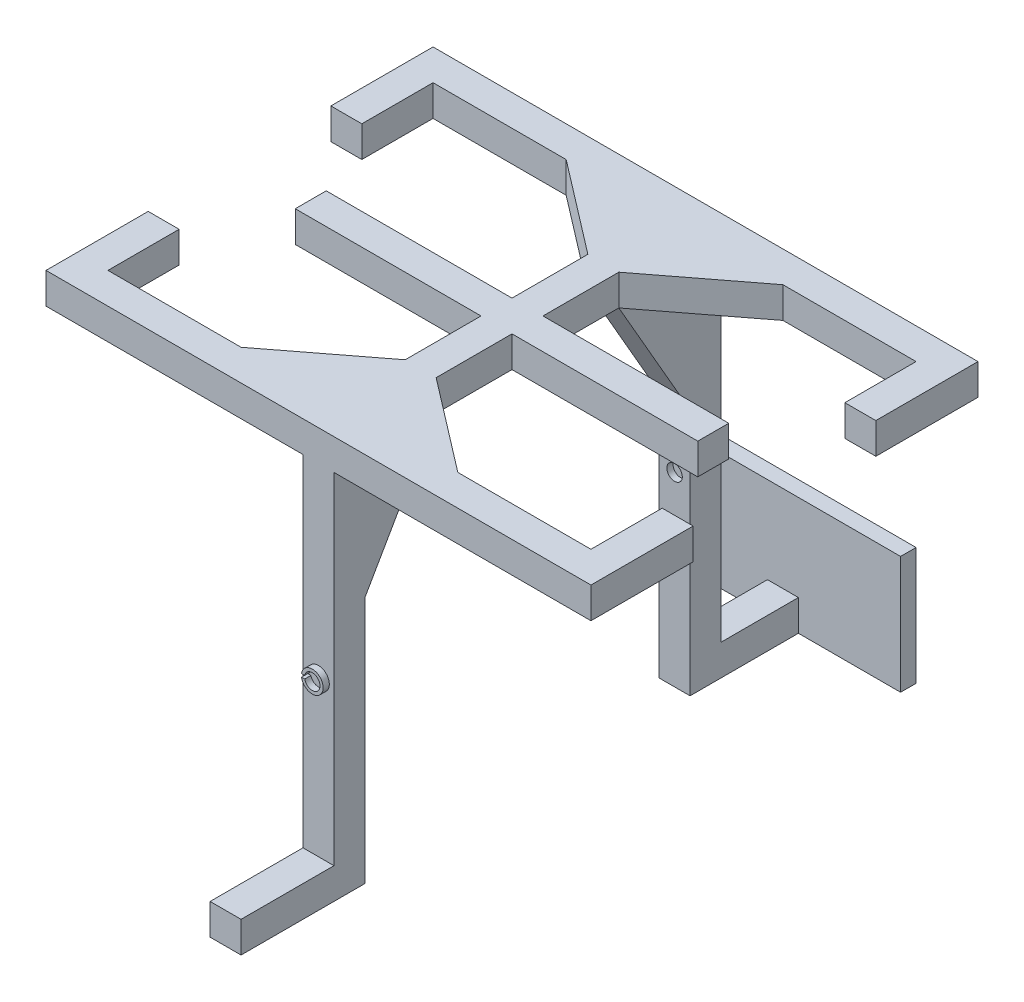
SolidWorks part; units mm, degrees
ref_plane "Front Plane" through (0, 0, 0) normal (0, 0, 1) x (1, 0, 0)
ref_plane "Top Plane" through (0, 0, 0) normal (0, 1, 0) x (1, 0, 0)
ref_plane "Right Plane" through (0, 0, 0) normal (1, 0, 0) x (0, 0, -1)
sketch "Sketch1" plane through (0, 0, 0) normal (0, 0, 1) x (1, 0, 0)
  line L1 (0, 0) -> (176, 0)
  line L2 (0, 0) -> (0, 10)
  line L3 (0, 10) -> (176, 10)
  line L4 (176, 0) -> (176, 10)
  dimension "D1" = 176
  dimension "D2" = 10
extrude "Boss-Extrude1" add sketch "Sketch1" along normal blind 10
sketch "Sketch2" plane through (0, 0, 0) normal (0, 0, -1) x (-1, 0, 0)
  line L0 (-88, 0) -> (-88, 10) construction
  line L2 (0, 0) -> (-176, 0) construction
  line L3 (-176, 10) -> (0, 10) construction
  line L9 (-83, 10) -> (-93, 10)
  line L10 (-83, 10) -> (-83, 0)
  line L11 (-83, 0) -> (-93, 0)
  line L12 (-93, 10) -> (-93, 0)
  line L13 (-83, 10) -> (-93, 0) construction
  line L14 (-83, 0) -> (-93, 10) construction
  point P6 (-88, 5)
  dimension "D1" = 10
extrude "Boss-Extrude2" add sketch "Sketch2" along normal blind 52.5
sketch "Sketch3" plane through (0, 0, 0) normal (0, 0, -1) x (-1, 0, 0)
  line L0 (-83, 10) -> (0, 10) construction
  line L1 (0, 0) -> (-10, 0)
  line L2 (0, 0) -> (0, 10)
  line L3 (0, 10) -> (-10, 10)
  line L4 (-10, 0) -> (-10, 10)
  line L5 (-83, 0) -> (-93, 0) construction
  line L6 (-176, 10) -> (-93, 10) construction
  line L7 (-176, 0) -> (-166, 0)
  line L8 (-176, 0) -> (-176, 10)
  line L9 (-176, 10) -> (-166, 10)
  line L10 (-166, 0) -> (-166, 10)
  dimension "D1" = 10
extrude "Boss-Extrude3" add sketch "Sketch3" along normal blind 23
mirror "Mirror6" about plane through (0, 0, -52.5) normal (0, 0, 1) of bodies 108 109
sketch "Sketch4" plane through (0, 0, 0) normal (0, -1, 0) x (1, 0, 0)
  line L0 (0, 10) -> (176, 10) construction
  line L1 (93, 0) -> (83, 0)
  line L2 (93, 0) -> (93, 10)
  line L3 (93, 10) -> (83, 10)
  line L4 (83, 0) -> (83, 10)
  line L5 (83, -52.5) -> (93, -52.5) construction
  line L6 (83, -105) -> (83, 0) construction
  line L7 (93, -105) -> (93, 0) construction
  line L8 (93, -105) -> (93, -115)
  line L9 (93, -115) -> (83, -115)
  line L10 (83, -105) -> (83, -115)
  line L11 (93, -105) -> (83, -105)
  dimension "D1" = 10
extrude "Boss-Extrude4" add sketch "Sketch4" along normal blind 120
sketch "Sketch13" plane through (83, 0, 0) normal (-1, 0, 0) x (0, 0, 1)
  line L0 (-105, 0) -> (-82, 0)
  line L1 (-105, 0) -> (0, 0) construction
  line L2 (-105, 0) -> (-105, -40)
  line L3 (-105, -120) -> (-105, 0) construction
  line L4 (-105, -40) -> (-82, 0)
  line L5 (0, -40) -> (0, 0)
  line L6 (0, -120) -> (0, 0) construction
  line L7 (0, 0) -> (-23, 0)
  line L8 (-23, 0) -> (0, -40)
extrude "Boss-Extrude5" add sketch "Sketch13" against normal blind 10
sketch "Sketch15" plane through (83, 0, 0) normal (-1, 0, 0) x (0, 0, 1)
  line L0 (-52.5, 10) -> (-52.5, 0) construction
  line L1 (-105, 10) -> (0, 10) construction
  line L2 (-82, 0) -> (-23, 0) construction
  point P6 (0, 0)
sketch "Sketch17" plane through (83, 0, 0) normal (-1, 0, 0) x (0, 0, 1)
  line L0 (-52.5, 0) -> (-52.5, 10) construction
  line L1 (-82, 0) -> (-23, 0) construction
  line L3 (-47.5, 10) -> (-57.5, 10)
  line L4 (-47.5, 10) -> (-47.5, 0)
  line L5 (-47.5, 0) -> (-57.5, 0)
  line L6 (-57.5, 10) -> (-57.5, 0)
  line L7 (-47.5, 10) -> (-57.5, 0) construction
  line L8 (-47.5, 0) -> (-57.5, 10) construction
  point P5 (-52.5, 5)
  dimension "D1" = 10
extrude "Boss-Extrude6" add sketch "Sketch17" along normal blind 20
sketch "Sketch18" plane through (0, 0, 0) normal (0, -1, 0) x (1, 0, 0)
  line L5 (71, -52.5) -> (65, -52.5)
  arc A1 (65, -52.5) -> (71, -52.5) centre (68, -52.5) ccw
revolve "Cut-Revolve2" cut sketch "Sketch18" angle 180 about L5
pattern_linear "LPattern1" count 3 spacing 20 along (-1, 0, 0) of "Boss-Extrude6", "Cut-Revolve2"
sketch "Sketch20" plane through (0, 0, 0) normal (0, -1, 0) x (1, 0, 0)
  line L0 (88, -23) -> (88, -82) construction
  line L1 (93, -23) -> (83, -23) construction
  line L2 (93, -82) -> (83, -82) construction
  line L3 (88, -52.5) -> (5.9948, -15.4171) construction
  line L4 (2.9948, -15.4171) -> (8.9948, -15.4171)
  arc A0 (2.9948, -15.4171) -> (8.9948, -15.4171) centre (5.9948, -15.4171) cw
  point P11 (5.9948, -15.4171)
sketch "Sketch23" plane through (93, 0, 0) normal (1, 0, 0) x (0, 0, -1)
  line L0 (52.5, 0) -> (52.5, 10) construction
  line L1 (82, 0) -> (23, 0) construction
  line L2 (105, 10) -> (0, 10) construction
  line L4 (57.5, 10) -> (47.5, 10)
  line L5 (57.5, 10) -> (57.5, 0)
  line L6 (57.5, 0) -> (47.5, 0)
  line L7 (47.5, 10) -> (47.5, 0)
  line L8 (57.5, 10) -> (47.5, 0) construction
  line L9 (57.5, 0) -> (47.5, 10) construction
  point P6 (52.5, 5)
  dimension "D1" = 10
extrude "Boss-Extrude7" add sketch "Sketch23" along normal blind 20
sketch "Sketch24" plane through (0, 0, 0) normal (0, -1, 0) x (1, 0, 0)
  line L5 (111, -52.5) -> (105, -52.5)
  arc A1 (105, -52.5) -> (111, -52.5) centre (108, -52.5) cw
revolve "Cut-Revolve3" cut sketch "Sketch24" angle 180 about L5
pattern_linear "LPattern2" count 3 spacing 20 along (1, 0, 0) of "Boss-Extrude7", "Cut-Revolve3"
sketch "Sketch25" plane through (0, 0, -115) normal (0, 0, -1) x (-1, 0, 0)
  line L0 (-83, -120) -> (-83, 0) construction
  line L1 (-93, -120) -> (-83, -120)
  line L2 (-93, -120) -> (-93, -110)
  line L3 (-93, -110) -> (-83, -110)
  line L4 (-83, -120) -> (-83, -110)
  dimension "D1" = 10
extrude "Boss-Extrude8" add sketch "Sketch25" along normal blind 30
sketch "Sketch27" plane through (0, 0, 10) normal (0, 0, 1) x (1, 0, 0)
  line L0 (83, -120) -> (83, 0) construction
  line L1 (93, -120) -> (83, -120)
  line L2 (93, -120) -> (93, -110)
  line L3 (93, -110) -> (83, -110)
  line L4 (83, -120) -> (83, -110)
  dimension "D1" = 10
extrude "Boss-Extrude10" add sketch "Sketch27" along normal blind 30
sketch "Sketch28" plane through (0, 0, -145) normal (0, 0, -1) x (-1, 0, 0)
  line L0 (-88, -120) -> (-88, -101) construction
  line L1 (-93, -120) -> (-83, -120) construction
  line L3 (-50, -82) -> (-126, -82)
  line L4 (-50, -82) -> (-50, -120)
  line L5 (-50, -120) -> (-126, -120)
  line L6 (-126, -82) -> (-126, -120)
  line L7 (-50, -82) -> (-126, -120) construction
  line L8 (-50, -120) -> (-126, -82) construction
  dimension "D1" = 76
extrude "Boss-Extrude11" add sketch "Sketch28" against normal blind 5
sketch "Sketch30" plane through (0, 0, 0) normal (0, -1, 0) x (1, 0, 0)
  line L0 (93, -105) -> (123, -105)
  line L1 (93, -105) -> (166, -105) construction
  line L2 (93, -105) -> (93, -82)
  line L3 (93, -82) -> (123, -105)
  line L4 (93, 0) -> (93, -23)
  line L5 (93, 0) -> (123, 0)
  line L6 (93, 0) -> (166, 0) construction
  line L7 (123, 0) -> (93, -23)
extrude "Boss-Extrude12" add sketch "Sketch30" against normal blind 10
pattern_circular "CirPattern2" count 2 every 180 about axis through (88, 0, -52.5) along (0, 1, 0) of "Boss-Extrude12"
sketch "Sketch31" plane through (0, 0, -115) normal (0, 0, -1) x (-1, 0, 0)
  line L0 (-88, -110) -> (-88, -60) construction
  line L1 (-83, -110) -> (-93, -110) construction
  circle A0 centre (-88, -60) radius 2.5
  circle A1 centre (-88, -60) radius 3.5
extrude "Boss-Extrude13" add sketch "Sketch31" along normal blind 2
sketch "Sketch32" plane through (0, 0, 10) normal (0, 0, 1) x (1, 0, 0)
  line L0 (88, -110) -> (88, -60) construction
  line L1 (93, -110) -> (83, -110) construction
  circle A0 centre (88, -60) radius 2.5
  circle A1 centre (88, -60) radius 3.5
extrude "Boss-Extrude14" add sketch "Sketch32" along normal blind 2
sketch "Sketch33" plane through (0, 0, -105) normal (0, 0, 1) x (1, 0, 0)
  line L0 (88, -120) -> (88, -60) construction
  line L1 (93, -120) -> (83, -120) construction
  circle A0 centre (88, -60) radius 2.5
extrude "Cut-Extrude1" cut sketch "Sketch33" against normal blind 2
sketch "Sketch34" plane through (0, 0, 0) normal (0, 0, -1) x (-1, 0, 0)
  line L0 (-88, -120) -> (-88, -60) construction
  line L1 (-83, -120) -> (-93, -120) construction
  circle A0 centre (-88, -60) radius 2.5
extrude "Cut-Extrude2" cut sketch "Sketch34" against normal blind 2
sketch "Sketch35" plane through (0, 0, 12) normal (0, 0, 1) x (1, 0, 0)
  line L1 (86.6943, -60.5) -> (84.3057, -60.5)
  line L2 (86.6943, -60.5) -> (86.6943, -59.5)
  line L3 (86.6943, -59.5) -> (84.3057, -59.5)
  line L4 (84.3057, -60.5) -> (84.3057, -59.5)
  line L5 (86.6943, -60.5) -> (84.3057, -59.5) construction
  line L6 (86.6943, -59.5) -> (84.3057, -60.5) construction
  circle A0 centre (88, -60) radius 2.5 construction
  point P0 (85.5, -60)
  dimension "D1" = 1
extrude "Cut-Extrude3" cut sketch "Sketch35" against normal blind 2
sketch "Sketch37" plane through (0, 0, -117) normal (0, 0, -1) x (-1, 0, 0)
  line L0 (-90.5, -60) -> (-91.5, -60) construction
  line L2 (-89.86, -59.5) -> (-92.14, -59.5)
  line L3 (-89.86, -59.5) -> (-89.86, -60.5)
  line L4 (-89.86, -60.5) -> (-92.14, -60.5)
  line L5 (-92.14, -59.5) -> (-92.14, -60.5)
  line L6 (-89.86, -59.5) -> (-92.14, -60.5) construction
  line L7 (-89.86, -60.5) -> (-92.14, -59.5) construction
  circle A0 centre (-88, -60) radius 2.5 construction
  circle A1 centre (-88, -60) radius 3.5 construction
  point P7 (-91, -60)
  dimension "D1" = 1
extrude "Cut-Extrude4" cut sketch "Sketch37" against normal blind 2
sketch "Sketch40" plane through (0, 0, 0) normal (0, -1, 0) x (1, 0, 0)
  line L0 (108, -52.5) -> (88, -52.5) construction
  line L1 (88, -52.5) -> (103.5584, -100.0177) construction
  line L2 (103.5584, -100.0177) -> (106.5584, -100.0177)
  line L3 (103.5584, -100.0177) -> (100.5584, -100.0177)
  arc A1 (100.5584, -100.0177) -> (106.5584, -100.0177) centre (103.5584, -100.0177) cw
  dimension "D1" = 50
revolve "Cut-Revolve4" cut sketch "Sketch40" angle 180 about L2
revolve "Cut-Revolve5" cut sketch "Sketch20" angle 180 about L4
sketch "Sketch42" plane through (0, -120, 0) normal (0, -1, 0) x (1, 0, 0)
  line L0 (88, 38) -> (88, 32)
  arc A0 (88, 38) -> (88, 32) centre (88, 35) ccw
revolve "Cut-Revolve8" cut sketch "Sketch42" angle 180 about L0
sketch "Sketch43" plane through (0, 0, 0) normal (0, -1, 0) x (1, 0, 0)
  line L0 (83, -47.5) -> (93, -57.5) construction
  line L2 (83, -57.5) -> (93, -47.5) construction
sketch "Sketch44" plane through (0, -120, 0) normal (0, -1, 0) x (1, 0, 0)
  line L0 (88, -107) -> (88, -113)
  arc A1 (88, -107) -> (88, -113) centre (88, -110) ccw
revolve "Cut-Revolve9" cut sketch "Sketch44" angle 180 about L0
